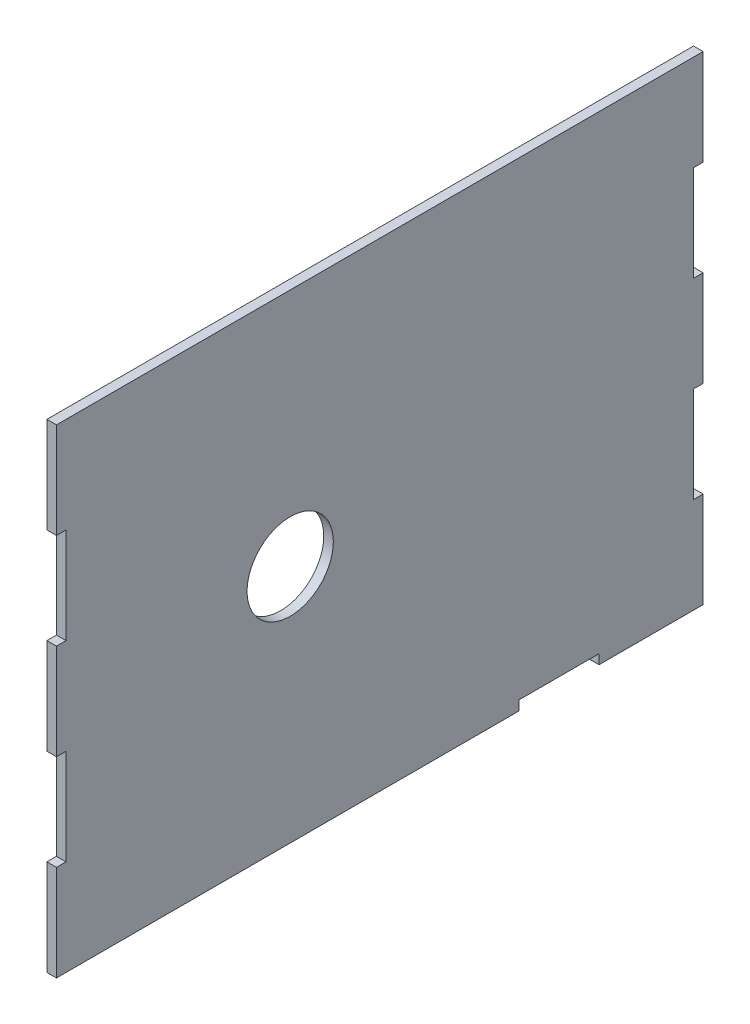
SolidWorks part; units mm, degrees
ref_plane "Front Plane" through (0, 0, 0) normal (0, 0, 1) x (1, 0, 0)
ref_plane "Top Plane" through (0, 0, 0) normal (0, 1, 0) x (1, 0, 0)
ref_plane "Right Plane" through (0, 0, 0) normal (1, 0, 0) x (0, 0, -1)
sketch "Sketch1" plane through (0, 0, 0) normal (1, 0, 0) x (0, 0, -1)
  line L1 (0, 0) -> (171.45, 0)
  line L2 (0, 0) -> (0, 127)
  line L3 (0, 127) -> (171.45, 127)
  line L4 (171.45, 0) -> (171.45, 127)
  dimension "D1" = 171.45
  dimension "D2" = 127
extrude "Boss-Extrude1" add sketch "Sketch1" along normal blind 2.54
sketch "Sketch2" plane through (2.54, 0, 0) normal (1, 0, 0) x (0, 0, -1)
  line L0 (0, 127) -> (0, 0) construction
  line L1 (2.54, 101.6) -> (0, 101.6)
  line L2 (2.54, 101.6) -> (2.54, 76.2)
  line L3 (2.54, 76.2) -> (0, 76.2)
  line L4 (0, 101.6) -> (0, 76.2)
  line L5 (171.45, 0) -> (171.45, 127) construction
  line L6 (0, 50.8) -> (2.54, 50.8)
  line L7 (0, 50.8) -> (0, 25.4)
  line L8 (0, 25.4) -> (2.54, 25.4)
  line L9 (2.54, 50.8) -> (2.54, 25.4)
  line L10 (171.45, 101.6) -> (168.91, 101.6)
  line L11 (171.45, 101.6) -> (171.45, 76.2)
  line L12 (171.45, 76.2) -> (168.91, 76.2)
  line L13 (168.91, 101.6) -> (168.91, 76.2)
  line L14 (171.45, 127) -> (0, 127) construction
  line L15 (171.45, 50.8) -> (168.91, 50.8)
  line L16 (171.45, 50.8) -> (171.45, 25.4)
  line L17 (171.45, 25.4) -> (168.91, 25.4)
  line L18 (168.91, 50.8) -> (168.91, 25.4)
  dimension "D1" = 25.4
  dimension "D2" = 25.4
  dimension "D3" = 25.4
  dimension "D4" = 25.4
  dimension "D5" = 2.54
  dimension "D6" = 2.54
  dimension "D7" = 2.54
  dimension "D8" = 2.54
  dimension "D9" = 25.4
  dimension "D10" = 25.4
  dimension "D11" = 25.4
  dimension "D12" = 25.4
extrude "Cut-Extrude1" cut sketch "Sketch2" against normal through all contours L2 L1 L4 L3 | L7 L6 L9 L8 | L16 L15 L18 L17 | L11 L10 L13 L12
sketch "Sketch3" plane through (2.54, 0, 0) normal (1, 0, 0) x (0, 0, -1)
  line L0 (171.45, 127) -> (0, 127) construction
  line L1 (0, 76.2) -> (0, 50.8) construction
  circle A0 centre (61.976, 63.5) radius 11.43
  dimension "D1" = 22.86
  dimension "D2" = 63.5
  dimension "D3" = 61.976
extrude "Cut-Extrude2" cut sketch "Sketch3" against normal through all contours A0
sketch "Sketch4" plane through (2.54, 0, 0) normal (1, 0, 0) x (0, 0, -1)
  line L0 (0, 0) -> (171.45, 0) construction
  line L1 (143.8487, 0) -> (122.682, 0)
  line L2 (143.8487, 0) -> (143.8487, 2.54)
  line L3 (143.8487, 2.54) -> (122.682, 2.54)
  line L4 (122.682, 0) -> (122.682, 2.54)
  line L5 (0, 25.4) -> (0, 0) construction
  dimension "D1" = 21.1667
  dimension "D2" = 2.54
  dimension "D3" = 122.682
extrude "Cut-Extrude3" cut sketch "Sketch4" against normal through all contours L2 L1 L4 L3
equation "\"D1@Boss-Extrude1\" = \"Matterial_Thickness\""
equation "\"D6@Sketch2\" = \"Matterial_Thickness\""
equation "\"D5@Sketch2\" = \"Matterial_Thickness\""
equation "\"D7@Sketch2\"= \"Matterial_Thickness\""
equation "\"D8@Sketch2\" = \"Matterial_Thickness\""
equation "\"Matterial_Thickness\"= \"GMaterial\""
equation "\"D2@Sketch4\"=\"Matterial_Thickness\""
equation "\"GMaterial\"= \"Foamcore\""
equation "\"MDF\" = 0.3in"
equation "\"Foamcore\"= 0.1in"
